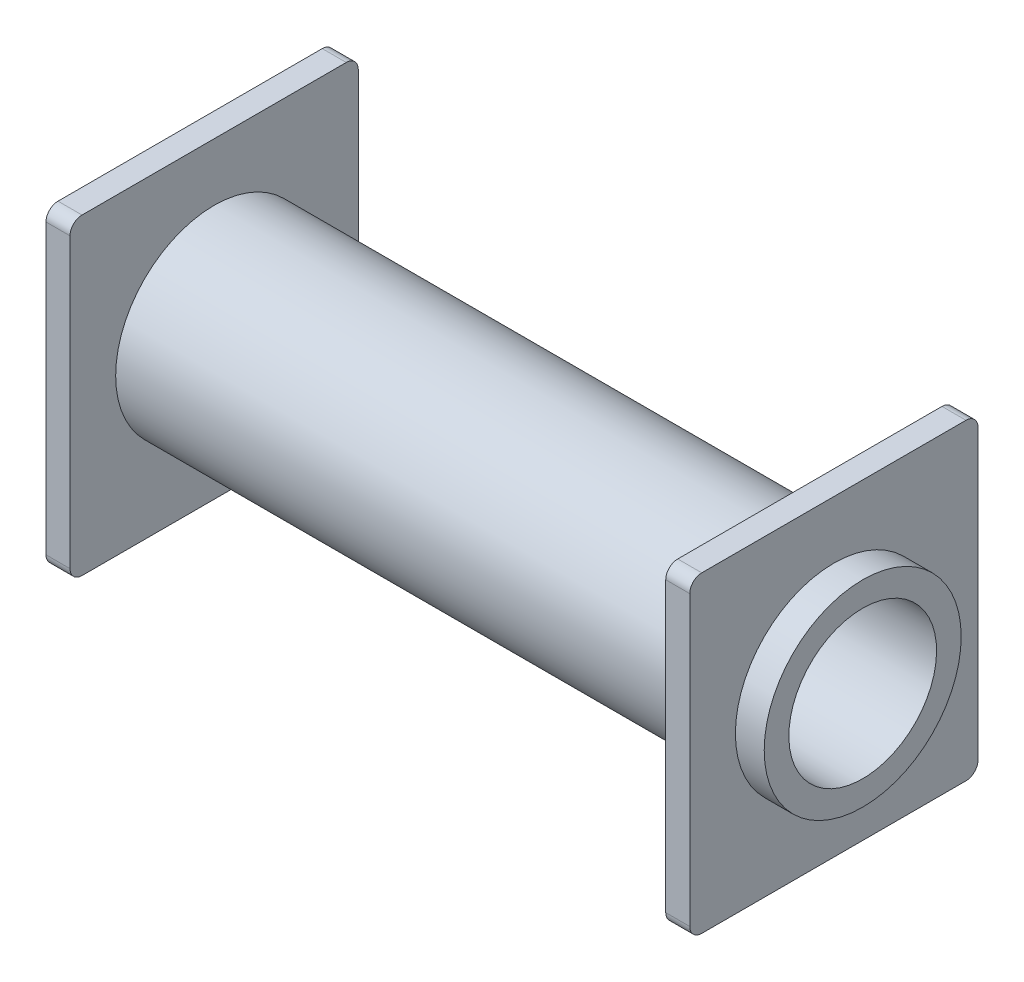
SolidWorks part; units mm, degrees
ref_plane "Alzado" through (0, 0, 0) normal (0, 0, 1) x (1, 0, 0)
ref_plane "Planta" through (0, 0, 0) normal (0, 1, 0) x (1, 0, 0)
ref_plane "Vista lateral" through (0, 0, 0) normal (1, 0, 0) x (0, 0, -1)
sketch "Croquis1" plane through (0, 0, 0) normal (0, 0, 1) x (1, 0, 0)
  line L1 (-14, 0) -> (14, 0)
  line L2 (-14, 0) -> (-14, 4.1)
  line L3 (-14, 4.1) -> (14, 4.1)
  line L4 (14, 0) -> (14, 4.1)
  point P4 (0, 0)
  dimension "D1" = 4.1
  dimension "D2" = 28
revolve "Revolución1" add sketch "Croquis1" angle 360 about L1
ref_plane "Plano1" through (11.8, 0, 0) normal (1, 0, 0) x (0, 0, -1)
sketch "Croquis3" plane through (11.8, 0, 0) normal (1, 0, 0) x (0, 0, -1)
  line L0 (-6, 6.5) -> (6, -6.5) construction
  line L1 (-6, 6.5) -> (6, 6.5)
  line L2 (-6, 6.5) -> (-6, -6.5)
  line L3 (-6, -6.5) -> (6, -6.5)
  line L4 (6, 6.5) -> (6, -6.5)
  point P4 (0, 0)
  dimension "D1" = 12
  dimension "D2" = 13
extrude "Saliente-Extruir1" add sketch "Croquis3" along normal blind 1
sketch "Croquis4" plane through (-14, 0, 0) normal (-1, 0, 0) x (0, 0, 1)
  line L0 (-6, 6.5) -> (6, 6.5) construction
  line L1 (-6, -6.5) -> (-6, 6.5) construction
  line L2 (6, -6.5) -> (-6, -6.5) construction
  line L3 (6, 6.5) -> (6, -6.5) construction
  line L4 (-6, 6.5) -> (6, 6.5)
  line L5 (-6, -6.5) -> (-6, 6.5)
  line L6 (6, -6.5) -> (-6, -6.5)
  line L7 (6, 6.5) -> (6, -6.5)
extrude "Saliente-Extruir2" add sketch "Croquis4" against normal blind 1
fillet "Redondeo1" radius 0.5 8 edges at (-13.5, -6.5, -6) (-13.5, -6.5, 6) (-13.5, 6.5, -6) (-13.5, 6.5, 6) (12.3, -6.5, -6) (12.3, -6.5, 6) (12.3, 6.5, -6) (12.3, 6.5, 6)
sketch "Croquis5" plane through (14, 0, 0) normal (1, 0, 0) x (0, 0, -1)
  circle A0 centre (0, 0) radius 3.075
  dimension "D1" = 6.15
extrude "Cortar-Extruir1" cut sketch "Croquis5" against normal up to next
